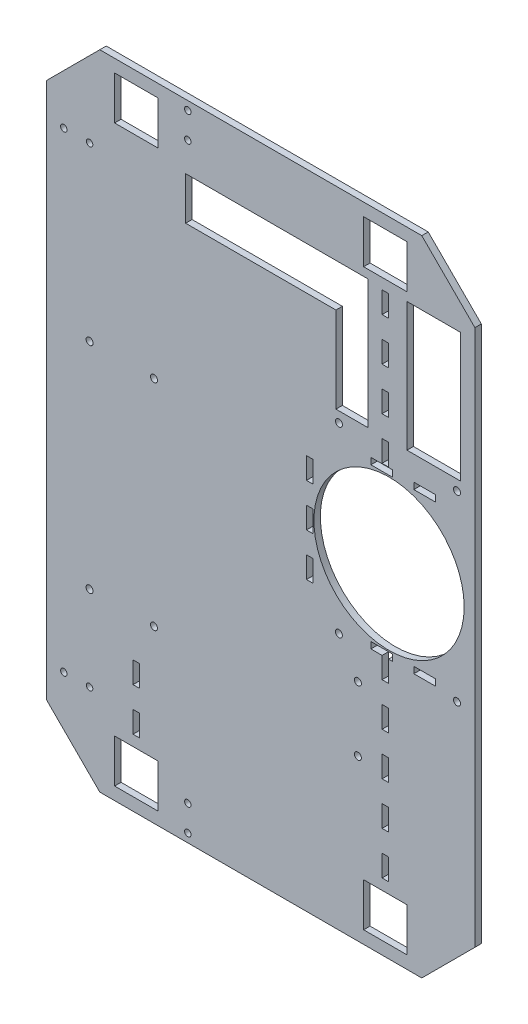
SolidWorks part; units mm, degrees
material "Alliage 1060"
ref_plane "Plan de dessus" through (0, 0, 0) normal (0, 0, 1) x (1, 0, 0)
ref_plane "Plan de droite" through (0, 0, 0) normal (0, 1, 0) x (1, 0, 0)
ref_plane "Plan de face" through (0, 0, 0) normal (1, 0, 0) x (0, 0, -1)
sketch "Esquisse1" plane through (0, 0, 0) normal (0, 0, 1) x (1, 0, 0)
  line L0 (0, 0) -> (-150, 0)
  line L1 (-150, 0) -> (-174.7487, 24.7487)
  line L2 (-174.7487, 24.7487) -> (-174.7487, 274.7487)
  line L3 (-174.7487, 274.7487) -> (-150, 299.4975)
  line L4 (-150, 299.4975) -> (0, 299.4975)
  line L5 (0, 299.4975) -> (24.7487, 274.7487)
  line L6 (24.7487, 274.7487) -> (24.7487, 24.7487)
  line L7 (24.7487, 24.7487) -> (0, 0)
  line L9 (-150, 299.4975) -> (0, 299.4975)
  line L10 (-174.7487, 274.7487) -> (-174.7487, 24.7487)
  line L12 (24.7487, 274.7487) -> (24.7487, 24.7487)
  dimension "D1" = 250
  dimension "D2" = 35
  dimension "D3" = 135
  dimension "D4" = 150
extrude "Base" add sketch "Esquisse1" along normal blind 3 contours L7 L6 L5 L4 L3 L2 L1 L0
sketch "Esquisse3" plane through (0, 0, 3) normal (0, 0, 1) x (1, 0, 0)
  line L0 (-174.7487, 24.7487) -> (-174.7487, 274.7487) construction
  line L1 (-143.0987, 5.9) -> (-122.8987, 5.9)
  line L2 (-143.0987, 5.9) -> (-143.0987, 26.1)
  line L3 (-143.0987, 26.1) -> (-122.8987, 26.1)
  line L4 (-122.8987, 5.9) -> (-122.8987, 26.1)
  line L5 (0, 0) -> (-150, 0) construction
  dimension "D1" = 20.2
  dimension "D2" = 31.65
  dimension "D3" = 5.9
extrude "Enlèv. mat.-Extru.1" cut sketch "Esquisse3" against normal through all
pattern_linear "Répétition linéaire1" count 2 spacing 267.5 along (0, 1, 0) count 2 spacing 116 along (1, 0, 0) of "Enlèv. mat.-Extru.1"
sketch "Esquisse4" plane through (0, 0, 3) normal (0, 0, 1) x (1, 0, 0)
  line L0 (24.7487, 274.7487) -> (24.7487, 24.7487) construction
  line L1 (-150, 299.4975) -> (0, 299.4975) construction
  circle A0 centre (-15.2513, 159.4975) radius 35
  dimension "D1" = 70
  dimension "D2" = 40
  dimension "D3" = 140
extrude "Enlèv. mat.-Extru.2" cut sketch "Esquisse4" against normal through all
sketch "Esquisse5" plane through (0, 0, 3) normal (0, 0, 1) x (1, 0, 0)
  line L0 (24.7487, 274.7487) -> (24.7487, 24.7487) construction
  line L1 (0, 0) -> (-150, 0) construction
  circle A0 centre (16.3987, 119.65) radius 1.625
  dimension "D1" = 3.25
  dimension "D2" = 8.35
  dimension "D3" = 119.65
extrude "Enlèv. mat.-Extru.3" cut sketch "Esquisse5" against normal up to next (3 mm away)
pattern_linear "Répétition linéaire2" count 2 spacing 85 along (0, 1, 0) count 2 spacing 55 along (-1, 0, 0) of "Enlèv. mat.-Extru.3"
sketch "Esquisse6" plane through (0, 0, 3) normal (0, 0, 1) x (1, 0, 0)
  line L0 (-150, 299.4975) -> (0, 299.4975) construction
  line L1 (-110, 269.4975) -> (-40, 269.4975)
  line L2 (-110, 269.4975) -> (-110, 249.4975)
  line L3 (-110, 249.4975) -> (-40, 249.4975)
  line L5 (-6.8987, 269.4975) -> (-6.8987, 209.4975)
  line L6 (-40, 269.4975) -> (-25, 269.4975)
  line L8 (-40, 209.4975) -> (-25, 209.4975)
  line L9 (-25, 269.4975) -> (-25, 209.4975)
  line L10 (-6.8987, 209.4975) -> (18.1013, 209.4975)
  line L11 (18.1013, 209.4975) -> (18.1013, 269.4975)
  line L12 (18.1013, 269.4975) -> (-6.8987, 269.4975)
  line L13 (-40, 249.4975) -> (-40, 209.4975)
  line L14 (-6.8987, 273.4) -> (-6.8987, 293.6) construction
  point P6 (-75, 299.4975)
  point P7 (-75, 269.4975)
  dimension "D1" = 70
  dimension "D2" = 20
  dimension "D3" = 30
  dimension "D4" = 60
  dimension "D5" = 15
  dimension "D6" = 25
extrude "Enlèv. mat.-Extru.4" cut sketch "Esquisse6" against normal up to next
sketch "Esquisse8" plane through (0, 0, 3) normal (0, 0, 1) x (1, 0, 0)
  line L0 (-109, 295.4975) -> (-109, 283.4975) construction
  line L1 (-150, 299.4975) -> (0, 299.4975) construction
  line L2 (-166.7487, 259.4975) -> (-154.7487, 259.4975) construction
  line L3 (-174.7487, 149.7487) -> (24.7487, 149.7487) construction
  line L4 (-174.7487, 24.7487) -> (-174.7487, 274.7487) construction
  line L5 (24.7487, 274.7487) -> (24.7487, 24.7487) construction
  line L7 (-75, 299.4975) -> (-75, 0) construction
  line L11 (0, 0) -> (-150, 0) construction
  circle A0 centre (-109, 295.4975) radius 1.5
  circle A1 centre (-109, 283.4975) radius 1.5
  circle A2 centre (-166.7487, 259.4975) radius 1.5
  circle A3 centre (-154.7487, 259.4975) radius 1.5
  circle A4 centre (-109, 16) radius 1.5
  circle A5 centre (-109, 4) radius 1.5
  circle A6 centre (-154.7487, 40) radius 1.5
  circle A7 centre (-166.7487, 40) radius 1.5
  dimension "D1" = 3
  dimension "D2" = 3
  dimension "D3" = 3
  dimension "D4" = 3
  dimension "D6" = 4
  dimension "D9" = 8
  dimension "D5" = 12
  dimension "D7" = 12
  dimension "D8" = 40
  dimension "D10" = 34
extrude "Trous deguisement" cut sketch "Esquisse8" against normal blind 5
sketch "Sketch1" plane through (0, 0, 3) normal (0, 0, 1) x (1, 0, 0)
  line L0 (-16.9987, 26.1) -> (-16.9987, 5.9) construction
  line L1 (-6.8987, 26.1) -> (-27.0987, 26.1) construction
  line L2 (-27.0987, 5.9) -> (-6.8987, 5.9) construction
  line L3 (-16.9987, 31.1) -> (-16.9987, 41.1) construction
  line L4 (-18.4987, 31.1) -> (-15.4987, 31.1)
  line L5 (-18.4987, 31.1) -> (-18.4987, 41.1)
  line L6 (-18.4987, 41.1) -> (-15.4987, 41.1)
  line L7 (-15.4987, 31.1) -> (-15.4987, 41.1)
  dimension "D1" = 3
  dimension "D2" = 10
  dimension "D3" = 5
extrude "Cut-Extrude1" cut sketch "Sketch1" against normal through all
pattern_linear "LPattern1" count 5 spacing 20 along (0, 1, 0) of "Cut-Extrude1"
sketch "Sketch2" plane through (0, 0, 3) normal (0, 0, 1) x (1, 0, 0)
  line L0 (-132.9987, 31.1) -> (-132.9987, 41.1) construction
  line L1 (-134.4987, 31.1) -> (-131.4987, 31.1)
  line L2 (-134.4987, 31.1) -> (-134.4987, 41.1)
  line L3 (-134.4987, 41.1) -> (-131.4987, 41.1)
  line L4 (-131.4987, 31.1) -> (-131.4987, 41.1)
  line L5 (-132.9987, 26.1) -> (-132.9987, 5.9) construction
  line L6 (-122.8987, 26.1) -> (-143.0987, 26.1) construction
  line L7 (-143.0987, 5.9) -> (-122.8987, 5.9) construction
  dimension "D1" = 3
  dimension "D2" = 10
  dimension "D3" = 5
extrude "Cut-Extrude2" cut sketch "Sketch2" against normal through all
pattern_linear "LPattern2" count 2 spacing 20 along (0, 1, 0) of "Cut-Extrude2"
sketch "Sketch3" plane through (0, 0, 3) normal (0, 0, 1) x (1, 0, 0)
  line L0 (-27.0987, 273.4) -> (-6.8987, 273.4) construction
  line L1 (-18.4987, 268.4) -> (-15.4987, 268.4)
  line L2 (-18.4987, 268.4) -> (-18.4987, 258.4)
  line L3 (-18.4987, 258.4) -> (-15.4987, 258.4)
  line L4 (-15.4987, 268.4) -> (-15.4987, 258.4)
  line L5 (-15.4987, 91.1) -> (-15.4987, 101.1) construction
  dimension "D1" = 10
  dimension "D2" = 3
  dimension "D3" = 5
extrude "Cut-Extrude3" cut sketch "Sketch3" against normal through all
pattern_linear "LPattern3" count 4 spacing 20 along (0, -1, 0) of "Cut-Extrude3"
sketch "Esquisse9" plane through (0, 0, 3) normal (0, 0, 1) x (1, 0, 0)
  line L0 (-174.7487, 24.7487) -> (-174.7487, 274.7487) construction
  line L1 (-150, 299.4975) -> (0, 299.4975) construction
  circle A0 centre (-154.7487, 179.4975) radius 1.625
  circle A1 centre (-124.7487, 179.4975) radius 1.625
  circle A2 centre (-154.7487, 79.4975) radius 1.625
  circle A3 centre (-124.7487, 79.4975) radius 1.625
  circle A5 centre (-29.7487, 74.65) radius 1.625
  circle A6 centre (-29.7487, 104.65) radius 1.625
  circle A9 centre (-38.6013, 119.65) radius 1.625 construction
  dimension "D2" = 3.25
  dimension "D3" = 3.25
  dimension "D7" = 3.25
  dimension "D8" = 3.25
  dimension "D10" = 3.25
  dimension "D1" = 30
  dimension "D4" = 20
  dimension "D5" = 120
  dimension "D6" = 30
  dimension "D9" = 100
  dimension "D11" = 30
  dimension "D16" = 15
extrude "Enlèv. mat.-Extru.5" cut sketch "Esquisse9" against normal blind 10
sketch "Esquisse10" plane through (0, 0, 3) normal (0, 0, 1) x (1, 0, 0)
  line L0 (24.7487, 122.4) -> (6.2987, 122.4) construction
  line L5 (24.7487, 274.7487) -> (24.7487, 24.7487) construction
  line L6 (0, 0) -> (-150, 0) construction
  line L11 (-3.7013, 120.9) -> (6.2987, 120.9)
  line L12 (-3.7013, 120.9) -> (-3.7013, 123.9)
  line L17 (-3.7013, 123.9) -> (6.2987, 123.9)
  line L18 (6.2987, 120.9) -> (6.2987, 123.9)
  line L19 (-23.7013, 120.9) -> (-13.7013, 120.9)
  line L20 (-23.7013, 120.9) -> (-23.7013, 123.9)
  line L21 (-23.7013, 123.9) -> (-13.7013, 123.9)
  line L22 (-13.7013, 120.9) -> (-13.7013, 123.9)
  line L27 (24.7487, 196.6975) -> (6.2987, 196.6975) construction
  line L28 (-150, 299.4975) -> (0, 299.4975) construction
  line L29 (-23.7013, 195.1975) -> (-13.7013, 195.1975)
  line L30 (-3.7013, 195.1975) -> (6.2987, 195.1975)
  line L31 (-3.7013, 195.1975) -> (-3.7013, 198.1975)
  line L32 (-3.7013, 198.1975) -> (6.2987, 198.1975)
  line L33 (6.2987, 195.1975) -> (6.2987, 198.1975)
  line L34 (-23.7013, 195.1975) -> (-23.7013, 198.1975)
  line L35 (-23.7013, 198.1975) -> (-13.7013, 198.1975)
  line L36 (-13.7013, 195.1975) -> (-13.7013, 198.1975)
  line L41 (-43.7013, 120.9) -> (-33.7013, 120.9) [skipped]
  line L42 (-43.7013, 120.9) -> (-43.7013, 123.9) [skipped]
  line L43 (-43.7013, 123.9) -> (-33.7013, 123.9) [skipped]
  line L44 (-33.7013, 120.9) -> (-33.7013, 123.9) [skipped]
  line L45 (-43.7013, 195.1975) -> (-33.7013, 195.1975) [skipped]
  line L46 (-43.7013, 195.1975) -> (-43.7013, 198.1975) [skipped]
  line L47 (-43.7013, 198.1975) -> (-33.7013, 198.1975) [skipped]
  line L48 (-33.7013, 195.1975) -> (-33.7013, 198.1975) [skipped]
  point P9 (6.2987, 122.4)
  point P27 (6.2987, 196.6975)
  dimension "D1" = 18.45
  dimension "D2" = 10
  dimension "D3" = 3
  dimension "D4" = 122.4
  dimension "D6" = 10
  dimension "D7" = 18.45
  dimension "D8" = 102.8
  dimension "D9" = 10
  dimension "D10" = 3
  dimension "D12" = 10
  dimension "D5" = 3
  dimension "D11" = 3
extrude "Enlèv. mat.-Extru.6" cut sketch "Esquisse10" against normal blind 3
sketch "Esquisse11" plane through (0, 0, 3) normal (0, 0, 1) x (1, 0, 0)
  line L0 (-23.7013, 123.9) -> (-23.7013, 133.9) construction
  line L1 (-23.7013, 133.9) -> (-50.7013, 133.9) construction
  line L2 (-50.7013, 153.9) -> (-53.7013, 153.9)
  line L3 (-50.7013, 133.9) -> (-53.7013, 133.9)
  line L4 (-50.7013, 133.9) -> (-50.7013, 143.9)
  line L5 (-50.7013, 143.9) -> (-53.7013, 143.9)
  line L6 (-53.7013, 133.9) -> (-53.7013, 143.9)
  line L7 (-50.7013, 153.9) -> (-50.7013, 163.9)
  line L8 (-50.7013, 163.9) -> (-53.7013, 163.9)
  line L9 (-53.7013, 153.9) -> (-53.7013, 163.9)
  line L10 (-50.7013, 173.9) -> (-53.7013, 173.9)
  line L11 (-50.7013, 173.9) -> (-50.7013, 183.9)
  line L12 (-50.7013, 183.9) -> (-53.7013, 183.9)
  line L13 (-53.7013, 173.9) -> (-53.7013, 183.9)
  dimension "D1" = 10
  dimension "D2" = 27
  dimension "D3" = 3
  dimension "D4" = 10
  dimension "D6" = 10
  dimension "D5" = 3
extrude "Enlèv. mat.-Extru.7" cut sketch "Esquisse11" against normal blind 3
